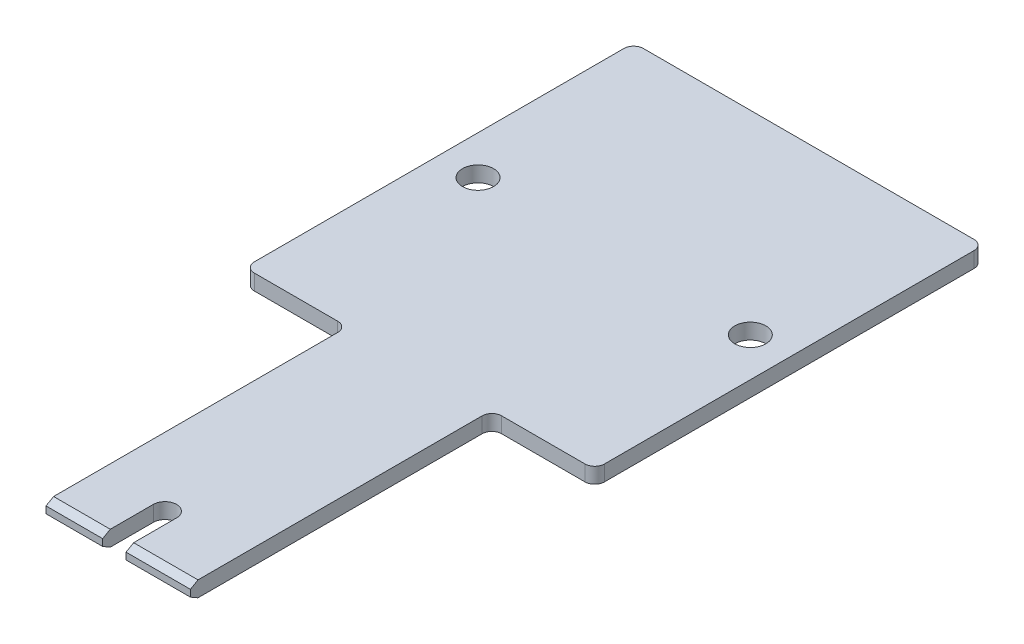
SolidWorks part; units mm, degrees
ref_plane "Front Plane" through (0, 0, 0) normal (0, 0, 1) x (1, 0, 0)
ref_plane "Top Plane" through (0, 0, 0) normal (0, 1, 0) x (1, 0, 0)
ref_plane "Right Plane" through (0, 0, 0) normal (1, 0, 0) x (0, 0, -1)
sketch "Sketch1" plane through (0, 0, 0) normal (0, 1, 0) x (1, 0, 0)
  line L0 (-7.425, 15.5) -> (-18, 15.5)
  line L1 (-7.425, 15.5) -> (7.425, 15.5) construction
  line L2 (-7.425, 15.5) -> (-7.425, -15.5)
  line L3 (-7.425, -15.5) -> (7.425, -15.5)
  line L4 (7.425, 15.5) -> (7.425, -15.5)
  line L5 (-7.425, 15.5) -> (7.425, -15.5) construction
  line L6 (-7.425, -15.5) -> (7.425, 15.5) construction
  line L7 (-18, 15.5) -> (-18, 55.5)
  line L8 (-18, 55.5) -> (18, 55.5)
  line L9 (18, 55.5) -> (18, 15.5)
  line L10 (18, 15.5) -> (7.425, 15.5)
  point P0 (0, 0)
  point P10 (0, 55.5)
  dimension "D1" = 14.85
  dimension "D2" = 31
  dimension "D3" = 36
  dimension "D4" = 40
extrude "Boss-Extrude1" add sketch "Sketch1" along normal blind 1.6
ref_plane "Plane1" through (-0.395, 0, 0) normal (-1, 0, 0) x (0, 0, 1)
chamfer "Chamfer1" distance 0.45 angle 60 2 edges at (0, 1.6, 15.5) (0, 0, 15.5)
fillet "Fillet1" radius 1 6 edges at (7.425, 0.8, -15.5) (18, 0.8, -15.5) (18, 0.8, -55.5) (-18, 0.8, -55.5) (-18, 0.8, -15.5) (-7.425, 0.8, -15.5)
sketch "Sketch2" plane through (0, 1.6, 0) normal (0, 1, 0) x (1, 0, 0)
  line L0 (7.425, -15.5) -> (-7.425, -15.5) construction
  line L1 (-1.595, -10.3) -> (0.805, -10.3) construction
  line L2 (-1.595, -10.3) -> (-1.595, -15.5)
  line L3 (-1.595, -15.5) -> (0.805, -15.5)
  line L4 (0.805, -10.3) -> (0.805, -15.5)
  line L5 (-1.595, -10.3) -> (0.805, -15.5) construction
  line L6 (-1.595, -15.5) -> (0.805, -10.3) construction
  line L7 (-0.395, 0.88) -> (-0.395, -0.88) construction
  arc A0 (0.805, -10.3) -> (-1.595, -10.3) centre (-0.395, -10.3) ccw
  point P0 (-0.395, -12.9)
  point P8 (0, 0)
  dimension "D1" = 2.4
  dimension "D2" = 5.2
extrude "Cut-Extrude1" cut sketch "Sketch2" against normal through all
hole_wizard "Ø3.2 (3.2) Diameter Hole1" positions "3DSketch1" profile "Sketch3" hole size "Ø3.2" standard "DIN"
sketch3d "3DSketch1"
  line L0 (17, 1.6, -55.5) -> (-17, 1.6, -55.5) construction
  line L1 (-18, 1.6, -54.5) -> (-18, 1.6, -16.5) construction
  line L2 (18, 1.6, -16.5) -> (18, 1.6, -54.5) construction
  point P0 (-14, 1.6, -35.5)
  point P2 (14, 1.6, -35.5)
  point P5 (0, 0, 0)
  dimension "D1" = 20
  dimension "D2" = 4
  dimension "D3" = 4
sketch "Sketch3" plane through (-14, 1.6, -35.5) normal (1, 0, 0) x (0, 0, 1)
  line L0 (0, 0) -> (0, 2.5614)
  line L1 (0, 2.5614) -> (1.6, 1.6)
  line L2 (1.6, 1.6) -> (1.6, 0)
  line L5 (1.6, 0) -> (0, 0)
  line L10 (0, 2.5614) -> (-1.6, 1.6) construction
  line L11 (0, -6.35) -> (0, 107.95) construction
  dimension "Hole Dia." = 3.2
  dimension "Hole Depth" = 1.6
  dimension "Drill Angle" = 118
